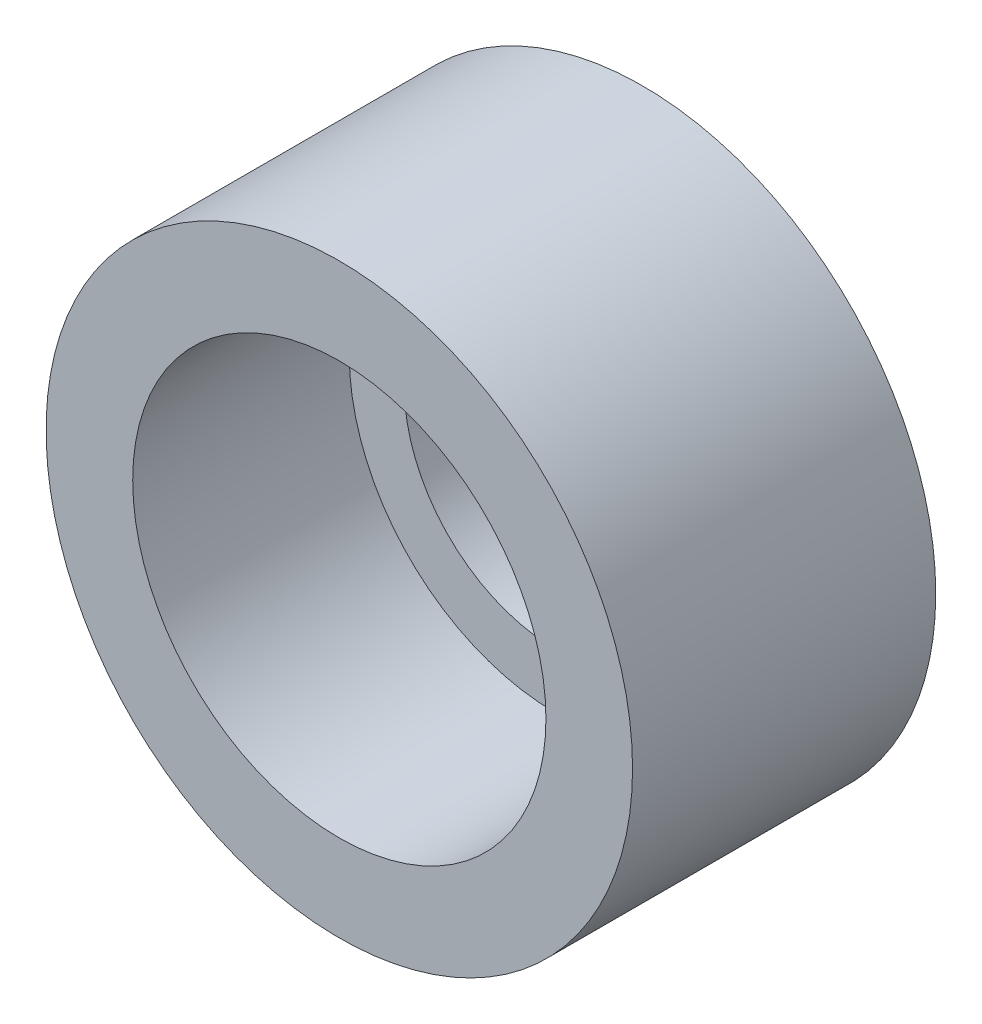
SolidWorks part; units mm, degrees
material "AISI Type 316L stainless steel"
ref_plane "Front Plane" through (0, 0, 0) normal (0, 0, 1) x (1, 0, 0)
ref_plane "Top Plane" through (0, 0, 0) normal (0, 1, 0) x (1, 0, 0)
ref_plane "Right Plane" through (0, 0, 0) normal (1, 0, 0) x (0, 0, -1)
sketch "Sketch1" plane through (0, 0, 0) normal (0, 0, 1) x (1, 0, 0)
  circle A0 centre (0, 0) radius 8.5985
  circle A1 centre (0, 0) radius 6.0585
  dimension "D1" = 17.197
  dimension "D2" = 2.54
extrude "Boss-Extrude1" add sketch "Sketch1" along normal blind 6.35 contours A1
sketch "Sketch2" plane through (0, 0, 0) normal (0, 0, 1) x (1, 0, 0)
  circle A0 centre (0, 0) radius 8.5985
extrude "Boss-Extrude2" add sketch "Sketch2" against normal blind 2.54
sketch "Sketch3" plane through (0, 0, -2.54) normal (0, 0, -1) x (-1, 0, 0)
  circle A0 centre (0, 0) radius 4.445
  dimension "D1" = 8.89
extrude "Cut-Extrude1" cut sketch "Sketch3" against normal through all
